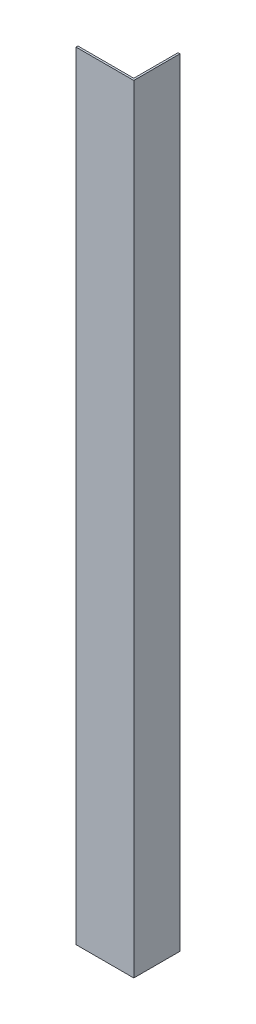
SolidWorks part; units mm, degrees
material "6061-T6 (SS)"
ref_plane "Alzado" through (0, 0, 0) normal (0, 0, 1) x (1, 0, 0)
ref_plane "Planta" through (0, 0, 0) normal (0, 1, 0) x (1, 0, 0)
ref_plane "Vista lateral" through (0, 0, 0) normal (1, 0, 0) x (0, 0, -1)
sketch "Sketch1" plane through (0, 0, 0) normal (0, 1, 0) x (1, 0, 0)
  line L0 (0, 0) -> (15, 0)
  line L1 (15, 0) -> (15, 12)
  line L2 (15, 12) -> (14.5, 12)
  line L3 (14.5, 12) -> (14.5, 0.5)
  line L4 (14.5, 0.5) -> (0, 0.5)
  line L5 (0, 0.5) -> (0, 0)
  dimension "D1" = 15
  dimension "D2" = 12
  dimension "D3" = 0.5
  dimension "D4" = 0.5
extrude "Boss-Extrude1" add sketch "Sketch1" along normal blind 202
